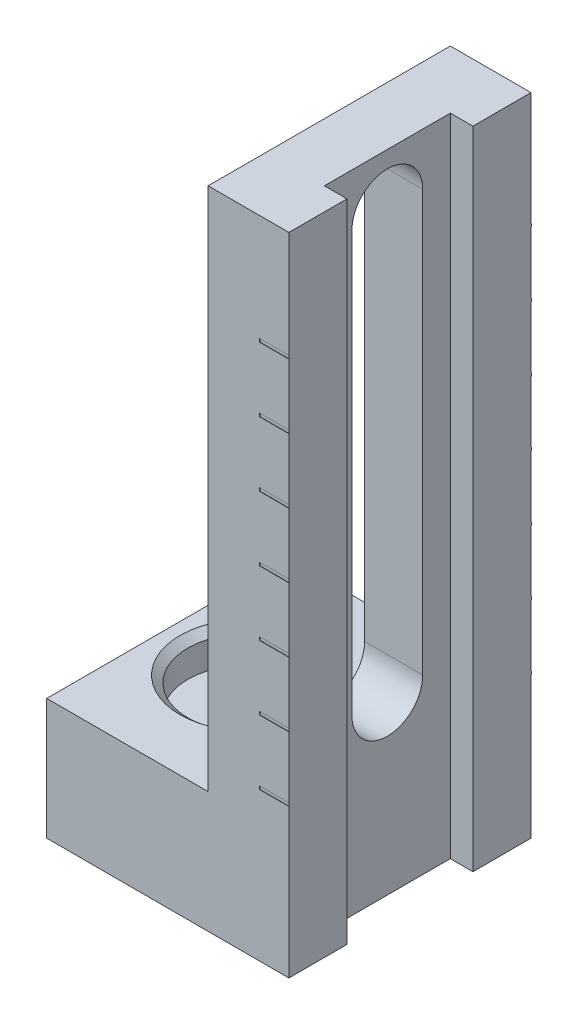
SolidWorks part; units mm, degrees
ref_plane "Front" through (0, 0, 0) normal (0, 0, 1) x (1, 0, 0)
ref_plane "Top" through (0, 0, 0) normal (0, 1, 0) x (1, 0, 0)
ref_plane "Right" through (0, 0, 0) normal (1, 0, 0) x (0, 0, -1)
sketch "Sketch1" plane through (0, 0, 0) normal (0, 0, 1) x (1, 0, 0)
  line L0 (0, 0) -> (19.05, 0)
  line L1 (19.05, 0) -> (19.05, 50.8)
  line L2 (19.05, 50.8) -> (12.7, 50.8)
  line L3 (0, 0) -> (0, 9.525)
  line L4 (12.7, 50.8) -> (12.7, 9.525)
  line L5 (12.7, 9.525) -> (0, 9.525)
extrude "Boss-Extrude1" add sketch "Sketch1" along normal blind 19.05
sketch "Sketch4" plane through (12.7, 0, 0) normal (-1, 0, 0) x (0, 0, 1)
  line L4 (9.525, 13.601) -> (9.525, 46.7002) construction
  line L5 (6.742, 13.601) -> (6.742, 46.7002)
  line L6 (12.308, 13.601) -> (12.308, 46.7002)
  arc A0 (6.742, 13.601) -> (12.308, 13.601) centre (9.525, 13.601) ccw
  arc A1 (12.308, 46.7002) -> (6.742, 46.7002) centre (9.525, 46.7002) ccw
  point P8 (9.525, 30.1506)
  point P13 (9.525, 46.7002)
  point P14 (9.525, 13.601)
extrude "Cut-Extrude1" cut sketch "Sketch4" against normal up to next
sketch "Sketch6" plane through (0, 50.8, 0) normal (0, 1, 0) x (1, 0, 0)
  line L0 (19.05, -4.572) -> (19.05, -14.478)
  line L1 (19.05, -19.05) -> (19.05, 0) construction
  line L2 (19.05, -4.572) -> (17.272, -4.572)
  line L4 (19.05, -14.478) -> (17.272, -14.478)
  line L5 (17.272, -4.572) -> (17.272, -14.478)
extrude "Cut-Extrude2" cut sketch "Sketch6" against normal up to surface (50.8 mm away) up to face at (9.525, 0, 9.525)
sketch "Sketch7" plane through (0, 9.525, 0) normal (0, 1, 0) x (1, 0, 0)
  line L0 (6.35, 0) -> (6.35, -19.05) construction
  line L2 (12.7, 0) -> (0, 0) construction
  line L3 (12.7, -19.05) -> (0, -19.05) construction
  line L4 (0, -9.525) -> (6.35, -9.525) construction
  line L5 (0, -19.05) -> (0, 0) construction
hole_wizard "CBORE for #8 Binding Head Machine Screw1" positions "Sketch10" profile "Sketch9" counterbore size "#8" standard "ANSI Inch" end condition up to next
sketch "Sketch10" plane through (0, 9.525, 0) normal (0, 1, 0) x (1, 0, 0)
  point P0 (6.35, -9.525)
sketch "Sketch9" plane through (6.35, 9.525, 9.525) normal (1, 0, 0) x (0, 0, 1)
  line L0 (0, 0) -> (0, 9.525)
  line L1 (0, 9.525) -> (2.2479, 9.525)
  line L3 (2.2479, 9.525) -> (2.2479, 2.667)
  line L4 (4.7625, 2.667) -> (2.2479, 2.667)
  line L5 (4.7625, 2.667) -> (4.7625, 0.5328)
  line L6 (4.7625, 0.5328) -> (5.3975, 0)
  line L7 (5.3975, 0) -> (0, 0)
  line L8 (-4.7625, 0.5328) -> (-5.3975, 0) construction
  line L11 (0, -6.35) -> (0, 107.95) construction
  dimension "Thru Hole Dia." = 4.4958
  dimension "Thru Hole Depth" = 9.525
  dimension "C'Bore Dia." = 9.525
  dimension "C'Bore Depth" = 2.667
  dimension "Near C'Sink Dia." = 10.795
  dimension "Near C'Sink Angle" = 100
sketch "Sketch11" plane through (0, 0, 19.05) normal (0, 0, 1) x (1, 0, 0)
  line L1 (19.05, 0) -> (19.05, 50.8) construction
  line L3 (19.05, 42.418) -> (16.7399, 42.418)
  line L4 (19.05, 42.418) -> (19.05, 42.168)
  line L5 (19.05, 42.168) -> (16.7399, 42.168)
  line L6 (16.7399, 42.418) -> (16.7399, 42.168)
extrude "Cut-Extrude3" cut sketch "Sketch11" against normal blind 0.02
pattern_linear "LPattern1" count 7 spacing 5.08 along (0, -1, 0) of "Cut-Extrude3"
sketch "Sketch13" plane through (0, 0, 0) normal (0, 0, -1) x (-1, 0, 0)
  line L1 (-19.05, 0) -> (-19.05, 50.8) construction
  line L3 (-19.05, 41.876) -> (-16.764, 41.876)
  line L4 (-19.05, 41.876) -> (-19.05, 41.622)
  line L5 (-19.05, 41.622) -> (-16.764, 41.622)
  line L6 (-16.764, 41.876) -> (-16.764, 41.622)
extrude "Boss-Extrude2" add sketch "Sketch13" along normal blind 0.02
pattern_linear "LPattern2" count 7 spacing 5.08 along (0, -1, 0) of "Boss-Extrude2"
